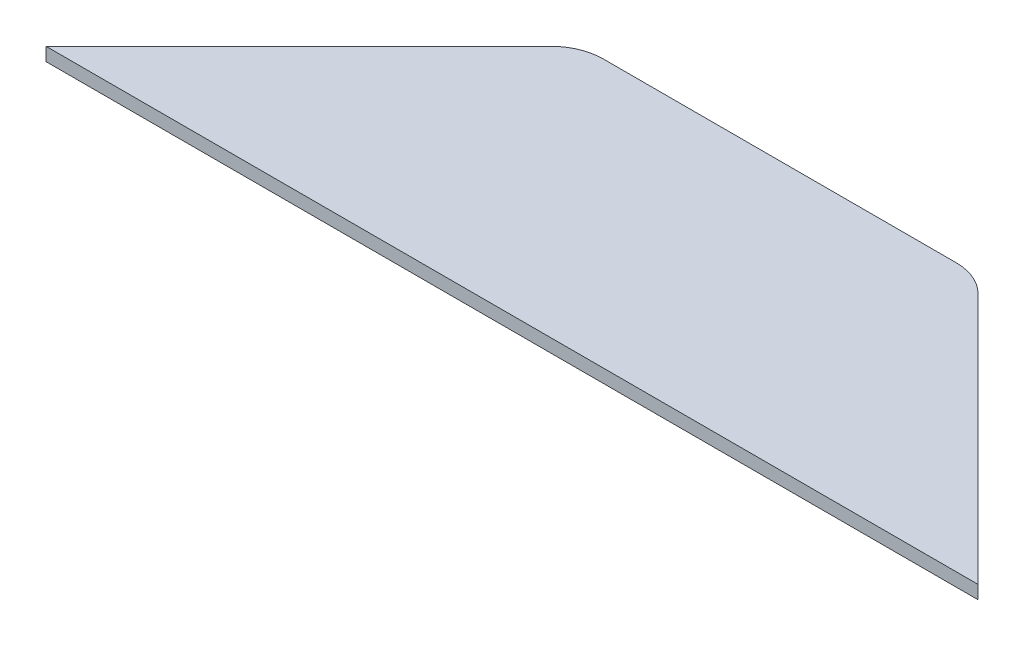
SolidWorks part; units mm, degrees
ref_plane "Front Plane" through (0, 0, 0) normal (0, 0, 1) x (1, 0, 0)
ref_plane "Top Plane" through (0, 0, 0) normal (0, 1, 0) x (1, 0, 0)
ref_plane "Right Plane" through (0, 0, 0) normal (1, 0, 0) x (0, 0, -1)
sketch "Sketch1" plane through (0, 0, 0) normal (0, 1, 0) x (1, 0, 0)
  line L0 (0, 0) -> (0, -56.3764) construction
  line L1 (21.1822, 0) -> (-21.1822, 0)
  line L2 (-25.6724, -1.8599) -> (-55.9435, -32.131)
  line L3 (25.6724, -1.8599) -> (55.9435, -32.131)
  line L10 (-55.9435, -32.131) -> (55.9435, -32.131)
  arc A0 (-21.1822, 0) -> (-25.6724, -1.8599) centre (-21.1822, -6.35) ccw
  arc A1 (25.6724, -1.8599) -> (21.1822, 0) centre (21.1822, -6.35) ccw
  point P9 (-23.8125, 0)
  point P12 (23.8125, 0)
  point P17 (0, 0)
  dimension "D4" = 6.35
  dimension "D1" = 135
  dimension "D2" = 47.625
  dimension "D3" = 32.131
extrude "Extrude1" add sketch "Sketch1" along normal blind 1.6002
